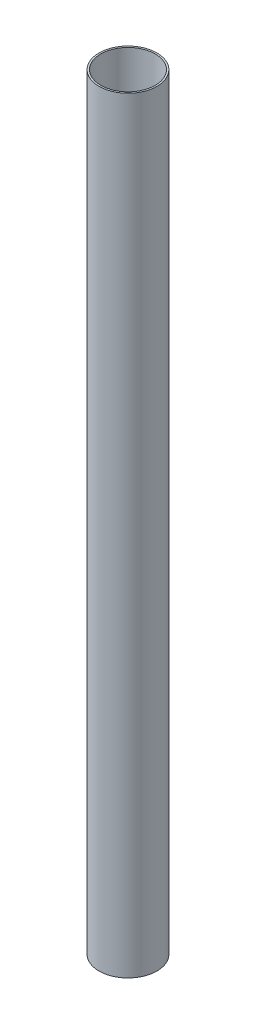
SolidWorks part; units mm, degrees
ref_plane "Спереди" through (0, 0, 0) normal (0, 0, 1) x (1, 0, 0)
ref_plane "Сверху" through (0, 0, 0) normal (0, 1, 0) x (1, 0, 0)
ref_plane "Справа" through (0, 0, 0) normal (1, 0, 0) x (0, 0, -1)
sketch "Эскиз1" plane through (0, 0, 0) normal (0, 1, 0) x (1, 0, 0)
  circle A0 centre (0, 0) radius 16
  circle A1 centre (0, 0) radius 17
  dimension "D1" = 34
  dimension "D2" = 32
extrude "Бобышка-Вытянуть1" add sketch "Эскиз1" along normal blind 450
